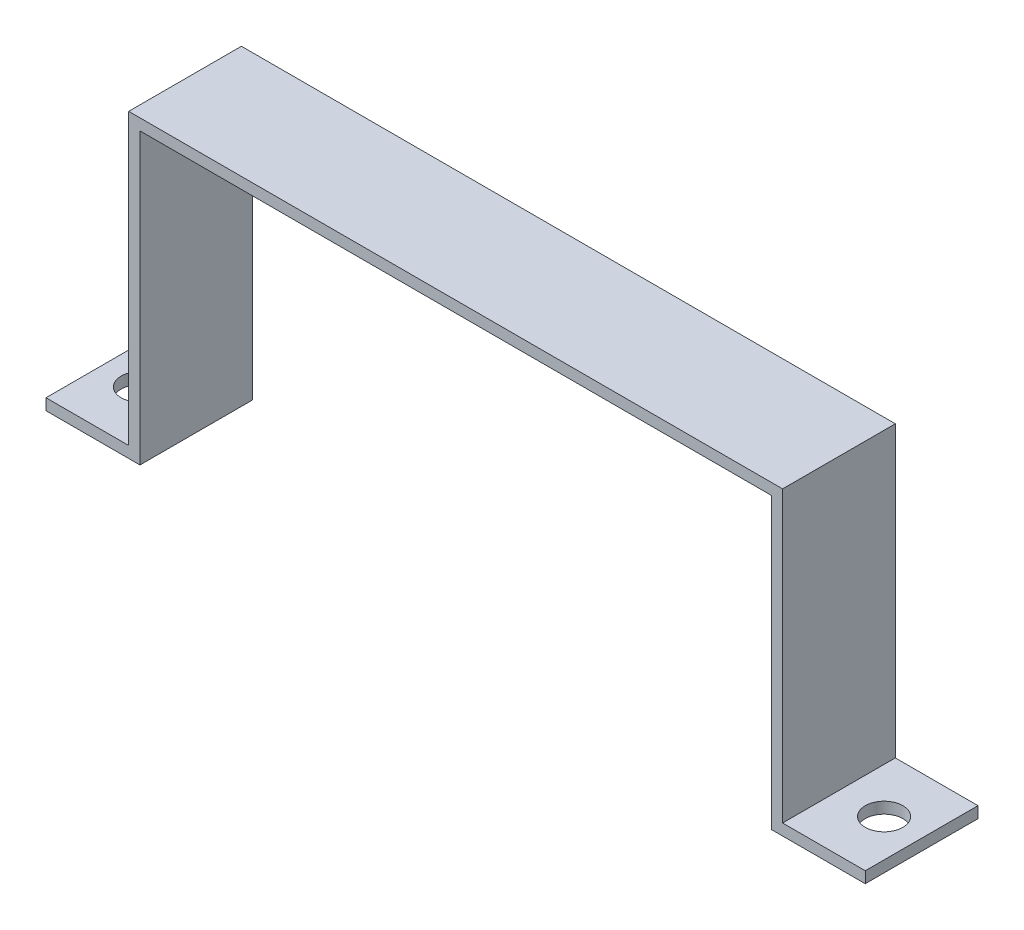
SolidWorks part; units mm, degrees
ref_plane "Front Plane" through (0, 0, 0) normal (0, 0, 1) x (1, 0, 0)
ref_plane "Top Plane" through (0, 0, 0) normal (0, 1, 0) x (1, 0, 0)
ref_plane "Right Plane" through (0, 0, 0) normal (1, 0, 0) x (0, 0, -1)
sketch "Sketch1" plane through (0, 0, 0) normal (0, 0, 1) x (1, 0, 0)
  line L0 (-84, 0) -> (84, 0) construction
  line L1 (-84, 0) -> (-84, 77)
  line L2 (-84, 77) -> (84, 77)
  line L3 (84, 77) -> (84, 0)
  line L4 (84, 0) -> (109, 0)
  line L5 (109, 0) -> (109, 3)
  line L6 (109, 3) -> (87, 3)
  line L7 (87, 3) -> (87, 80)
  line L8 (87, 80) -> (-87, 80)
  line L9 (-87, 80) -> (-87, 3)
  line L10 (-87, 3) -> (-109, 3)
  line L11 (-109, 3) -> (-109, 0)
  line L12 (-109, 0) -> (-84, 0)
  dimension "D1" = 3
  dimension "D2" = 3
  dimension "D3" = 3
  dimension "D4" = 3
  dimension "D5" = 77
  dimension "D6" = 168
  dimension "D7" = 84
  dimension "D8" = 25
  dimension "D9" = 25
  dimension "D10" = 3
extrude "Boss-Extrude1" add sketch "Sketch1" along normal blind 30
sketch "Sketch2" plane through (0, 3, 0) normal (0, 1, 0) x (1, 0, 0)
  line L0 (-87, 0) -> (-109, 0) construction
  line L2 (-87, -30) -> (-87, 0) construction
  line L3 (87, -30) -> (87, 0) construction
  line L4 (109, 0) -> (87, 0) construction
  circle A0 centre (-99, -15) radius 5
  circle A1 centre (99, -15) radius 5
  dimension "D2" = 10
  dimension "D6" = 10
  dimension "D1" = 15
  dimension "D3" = 12
  dimension "D4" = 12
  dimension "D5" = 15
extrude "Cut-Extrude1" cut sketch "Sketch2" against normal blind 30
